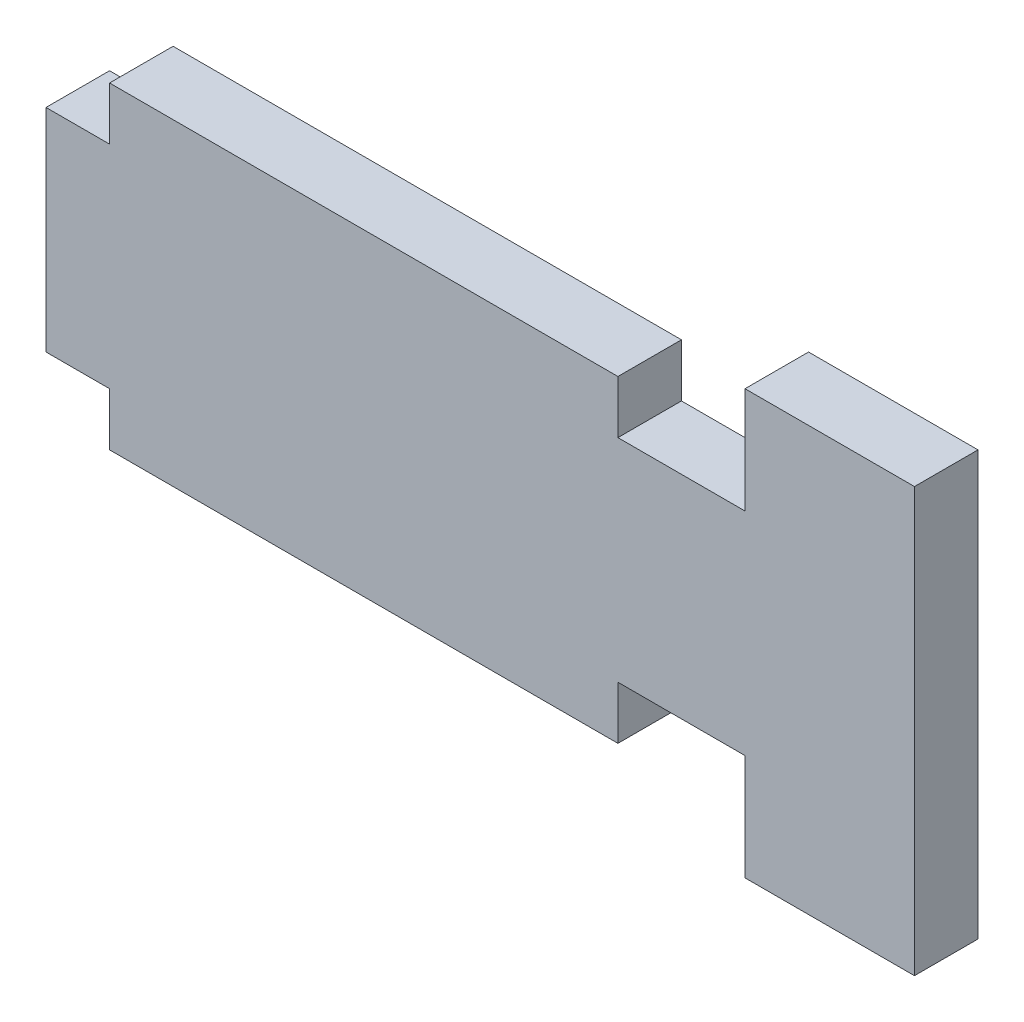
SolidWorks part; units mm, degrees
material "MDF"
ref_plane "Plano frontal" through (0, 0, 0) normal (0, 0, 1) x (1, 0, 0)
ref_plane "Plano superior" through (0, 0, 0) normal (0, 1, 0) x (1, 0, 0)
ref_plane "Plano direito" through (0, 0, 0) normal (1, 0, 0) x (0, 0, -1)
sketch "Esboço1" plane through (0, 0, 0) normal (0, 0, 1) x (1, 0, 0)
  line L0 (0, 0) -> (12, 0) construction
  line L1 (-12, -7.5) -> (12, -7.5)
  line L2 (-12, -7.5) -> (-12, 7.5)
  line L3 (-12, 7.5) -> (12, 7.5)
  line L4 (12, -7.5) -> (12, 7.5)
  line L5 (-12, -7.5) -> (12, 7.5) construction
  line L6 (-12, 7.5) -> (12, -7.5) construction
  line L11 (0, 0) -> (0, -7.5) construction
  line L12 (-15, -5) -> (-12, -5)
  line L17 (-15, -5) -> (-15, 5)
  line L18 (-15, 5) -> (-12, 5)
  line L19 (-12, -5) -> (-12, 5)
  line L20 (-15, -5) -> (-12, 5) construction
  line L21 (-15, 5) -> (-12, -5) construction
  line L26 (18, 5) -> (12, 5)
  line L27 (12, -5) -> (12, 5)
  line L28 (18, -5) -> (12, -5)
  line L29 (18, -5) -> (18, 5)
  line L30 (18, 5) -> (18, 10)
  line L31 (18, 10) -> (26, 10)
  line L32 (26, 10) -> (26, -10)
  line L33 (26, -10) -> (18, -10)
  line L34 (18, -5) -> (18, -10)
  point P0 (0, 0)
  point P6 (-13.5, 0)
  point P7 (26, 0)
  dimension "D5" = 6
  dimension "D1" = 15
  dimension "D2" = 3
  dimension "D3" = 10
  dimension "D4" = 24
  dimension "D6" = 8
  dimension "D7" = 20
extrude "Ressalto-extrusão1" add sketch "Esboço1" along normal blind 3
